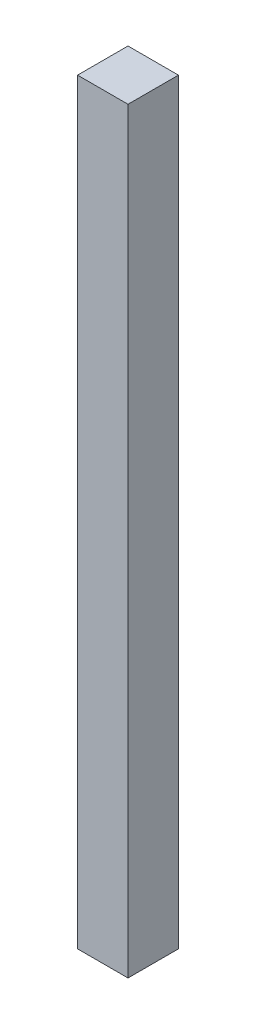
SolidWorks part; units mm, degrees
ref_plane "Front Plane" through (0, 0, 0) normal (0, 0, 1) x (1, 0, 0)
ref_plane "Top Plane" through (0, 0, 0) normal (0, 1, 0) x (1, 0, 0)
ref_plane "Right Plane" through (0, 0, 0) normal (1, 0, 0) x (0, 0, -1)
sketch "Sketch1" plane through (0, 0, 0) normal (0, 1, 0) x (1, 0, 0)
  line L1 (7.5, 7.5) -> (-7.5, 7.5)
  line L2 (7.5, 7.5) -> (7.5, -7.5)
  line L3 (7.5, -7.5) -> (-7.5, -7.5)
  line L4 (-7.5, 7.5) -> (-7.5, -7.5)
  line L5 (7.5, 7.5) -> (-7.5, -7.5) construction
  line L6 (7.5, -7.5) -> (-7.5, 7.5) construction
  point P0 (0, 0)
  dimension "D1" = 15
  dimension "D2" = 15
extrude "Boss-Extrude1" add sketch "Sketch1" along normal blind 225
